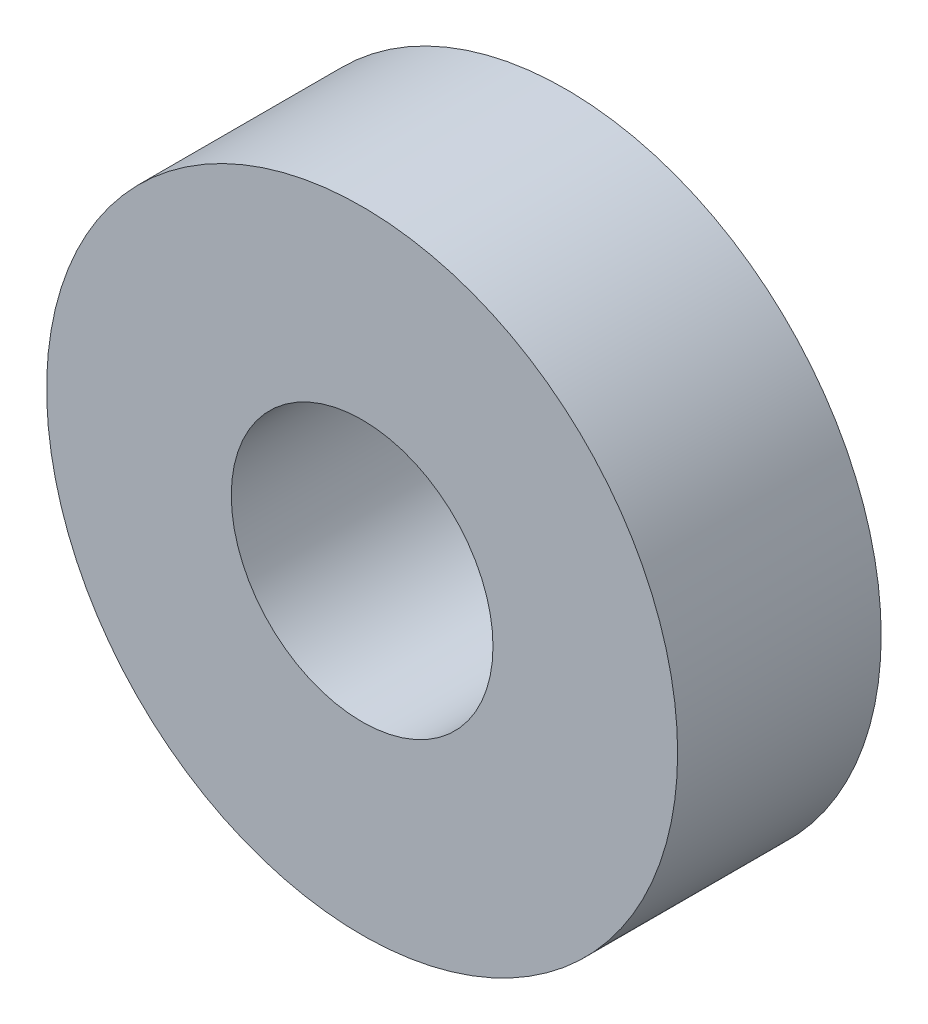
SolidWorks part; units mm, degrees
ref_plane "Front Plane" through (0, 0, 0) normal (0, 0, 1) x (1, 0, 0)
ref_plane "Top Plane" through (0, 0, 0) normal (0, 1, 0) x (1, 0, 0)
ref_plane "Right Plane" through (0, 0, 0) normal (1, 0, 0) x (0, 0, -1)
sketch "Sketch2" plane through (0, 0, -31.8925) normal (0, 0, 1) x (1, 0, 0)
  circle A0 centre (0, 0) radius 10.85
  circle A1 centre (-7.6, 0) radius 1.75
  circle A2 centre (7.6, 0) radius 1.75
  circle A3 centre (0, 0) radius 4.5
  circle A4 centre (0, 7.6) radius 1.75
  circle A5 centre (0, -7.6) radius 1.75
extrude "Boss-Extrude1" add sketch "Sketch2" along normal blind 7
sketch "Sketch3" plane through (0, 0, -24.8925) normal (0, 0, 1) x (1, 0, 0)
  circle A0 centre (0, 7.6) radius 1.75
  circle A1 centre (-7.6, 0) radius 1.75
  circle A2 centre (0, -7.6) radius 1.75
  circle A3 centre (7.6, 0) radius 1.75
extrude "Boss-Extrude2" add sketch "Sketch3" against normal blind 3
